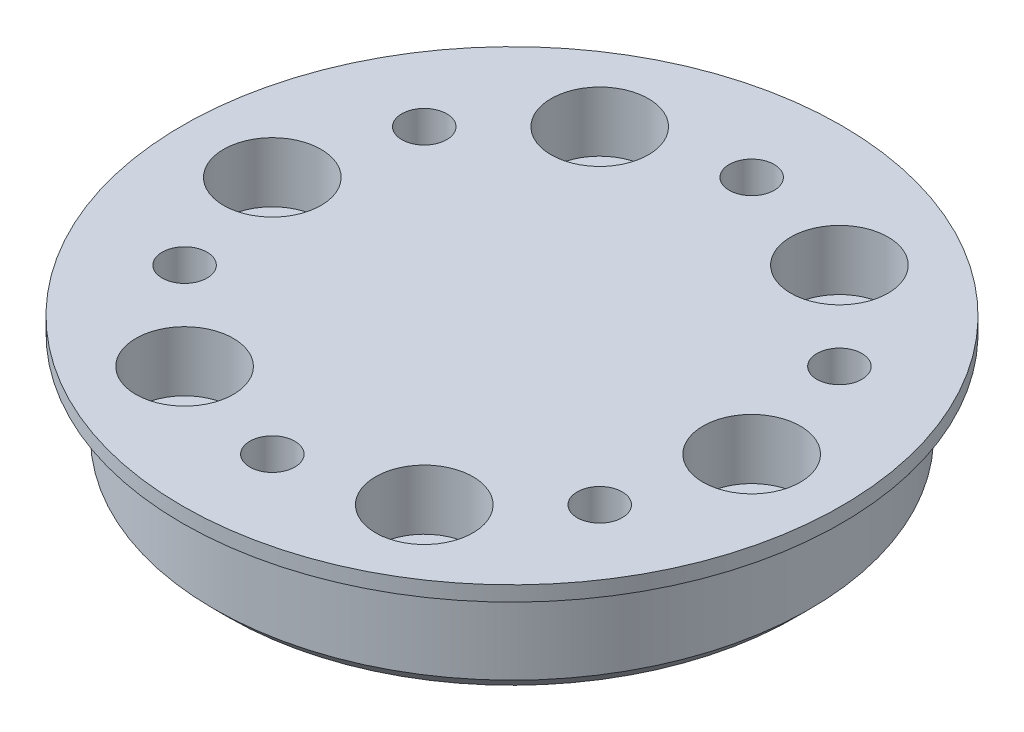
SolidWorks part; units mm, degrees
ref_plane "Front Plane" through (0, 0, 0) normal (0, 0, 1) x (1, 0, 0)
ref_plane "Top Plane" through (0, 0, 0) normal (0, 1, 0) x (1, 0, 0)
ref_plane "Right Plane" through (0, 0, 0) normal (1, 0, 0) x (0, 0, -1)
sketch "Sketch1" plane through (0, 0, 0) normal (0, 1, 0) x (1, 0, 0)
  circle A0 centre (0, 0) radius 19.9
  dimension "D1" = 39.8
extrude "Boss-Extrude1" add sketch "Sketch1" along normal blind 7
sketch "Sketch2" plane through (0, 7, 0) normal (0, 1, 0) x (1, 0, 0)
  circle A0 centre (0, 0) radius 22
  dimension "D1" = 44
extrude "Boss-Extrude2" add sketch "Sketch2" along normal blind 1
sketch "Sketch3" plane through (0, 8, 0) normal (0, 1, 0) x (1, 0, 0)
  circle A0 centre (0, 16) radius 1.5
  circle A2 centre (13.8564, 8) radius 1.5
  circle A4 centre (13.8564, -8) radius 1.5
  circle A6 centre (0, -16) radius 1.5
  circle A8 centre (-13.8564, -8) radius 1.5
  circle A10 centre (-13.8564, 8) radius 1.5
  circle A12 centre (-8, 13.8564) radius 1.6
  circle A13 centre (-16, 0) radius 1.6
  circle A14 centre (-8, -13.8564) radius 1.6
  circle A15 centre (8, -13.8564) radius 1.6
  circle A16 centre (16, 0) radius 1.6
  circle A17 centre (8, 13.8564) radius 1.6
  circle A18 centre (-8, 13.8564) radius 1.5 [skipped]
  circle A20 centre (-16, 0) radius 1.5 [skipped]
  circle A22 centre (-8, -13.8564) radius 1.5 [skipped]
  circle A24 centre (8, -13.8564) radius 1.5 [skipped]
  circle A26 centre (16, 0) radius 1.5 [skipped]
  circle A28 centre (8, 13.8564) radius 1.5 [skipped]
  point P12 (0, 0)
  point P28 (0, 0)
  dimension "D1" = 3
  dimension "D2" = 16
  dimension "D3" = 12
extrude "Cut-Extrude1" cut sketch "Sketch3" against normal through all
sketch "Sketch4" plane through (0, 8, 0) normal (0, 1, 0) x (1, 0, 0)
  circle A1 centre (-8, 13.8564) radius 3.25
  circle A3 centre (8, 13.8564) radius 3.25
  circle A4 centre (16, 0) radius 3.25
  circle A5 centre (8, -13.8564) radius 3.25
  circle A6 centre (-8, -13.8564) radius 3.25
  circle A7 centre (-16, 0) radius 3.25
  point P16 (0, 0)
  dimension "D1" = 6.5
  dimension "D2" = 6
extrude "Cut-Extrude2" cut sketch "Sketch4" against normal blind 4
chamfer "Chamfer1" distance 1 angle 45 1 edges at (0, 0, 19.9)
